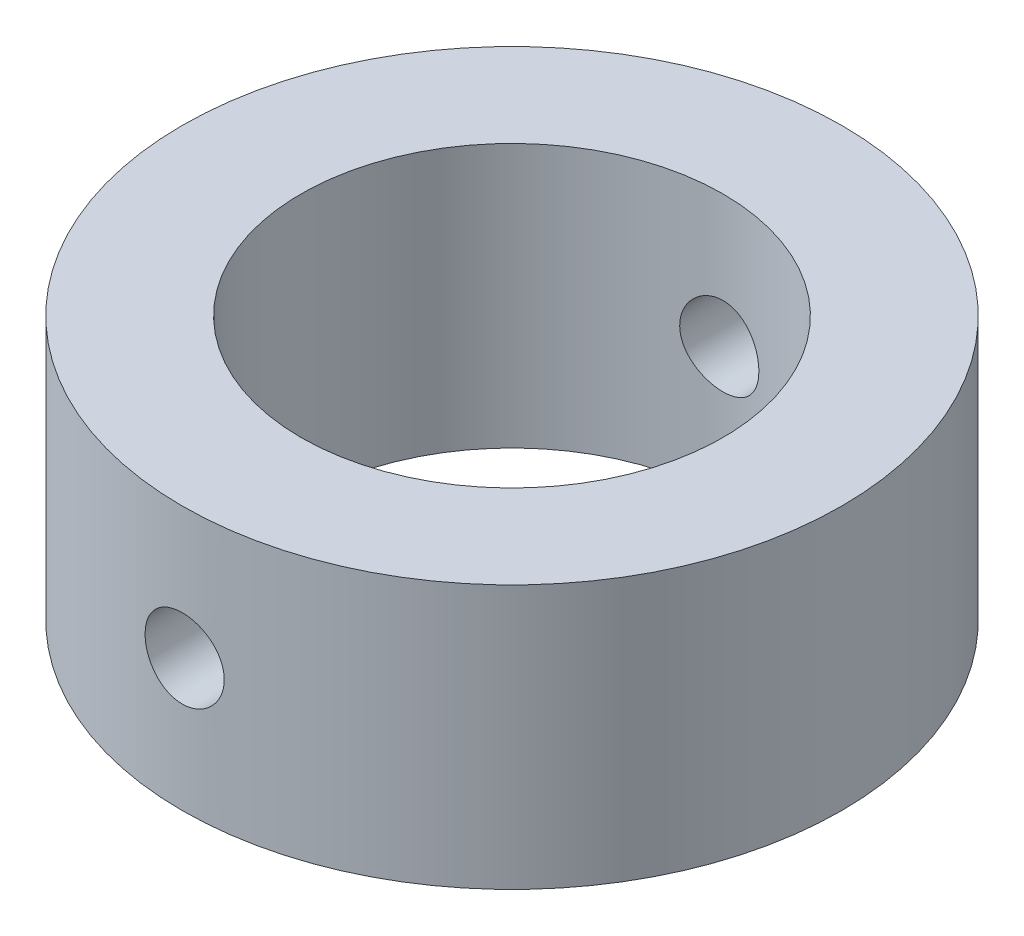
SolidWorks part; units mm, degrees
material "AISI 1020"
ref_plane "Front Plane" through (0, 0, 0) normal (0, 0, 1) x (1, 0, 0)
ref_plane "Top Plane" through (0, 0, 0) normal (0, 1, 0) x (1, 0, 0)
ref_plane "Right Plane" through (0, 0, 0) normal (1, 0, 0) x (0, 0, -1)
sketch "Sketch2" plane through (0, 0, 0) normal (0, 1, 0) x (1, 0, 0)
  circle A0 centre (0, 0) radius 12.5
  dimension "D1" = 25
extrude "Boss-Extrude1" add sketch "Sketch2" along normal blind 10
sketch "Sketch3" plane through (0, 10, 0) normal (0, 1, 0) x (1, 0, 0)
  circle A0 centre (0, 0) radius 8
  dimension "D1" = 16
extrude "Cut-Extrude1" cut sketch "Sketch3" against normal blind 10
sketch "Sketch5" plane through (0, 0, 0) normal (0, 0, 1) x (1, 0, 0)
  circle A0 centre (0, 5) radius 1.5
  dimension "D2" = 3
  dimension "D1" = 5
extrude "Cut-Extrude2" cut sketch "Sketch5" against normal through all both and the other way through all
scale "Scale1" scale about centroid uniform scaling yes scale factor 2
